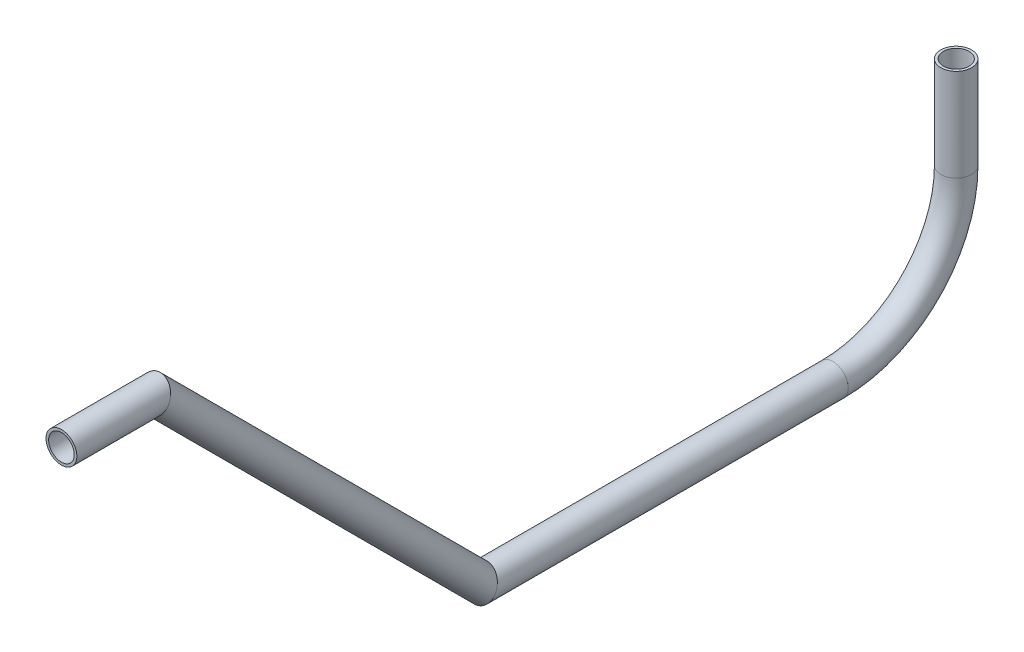
SolidWorks part; units mm, degrees
ref_plane "Front Plane" through (0, 0, 0) normal (0, 0, 1) x (1, 0, 0)
ref_plane "Top Plane" through (0, 0, 0) normal (0, 1, 0) x (1, 0, 0)
ref_plane "Right Plane" through (0, 0, 0) normal (1, 0, 0) x (0, 0, -1)
sketch "Sketch1" plane through (0, 0, 0) normal (1, 0, 0) x (0, 0, -1)
  line L0 (-303.593, 599.7633) -> (-265.493, 599.7633)
  line L2 (-265.493, 599.7633) -> (-130.9227, 465.193)
  line L3 (-130.9227, 465.193) -> (14.1198, 465.193)
  line L4 (64.9198, 554.093) -> (64.9198, 515.993)
  line L5 (-265.493, 599.7633) -> (-145.8362, 599.7633) construction
  arc A0 (14.1198, 465.193) -> (64.9198, 515.993) centre (14.1198, 515.993) ccw
  dimension "D1" = 45
  dimension "D2" = 50.8
  dimension "D3" = 38.1
  dimension "D4" = 38.1
other "Pipe 0.5 SCH 40(1)"
ref_plane "Plane1" through (0, 599.7633, 303.593) normal (0, 0, -1) x (0, 1, 0)
sketch "Sketch11" plane through (0, 599.7633, 303.593) normal (0, 0, -1) x (0, 1, 0)
  circle A0 centre (0, 0) radius 5.2832
  circle A1 centre (0, 0) radius 6.35
  point P5 (0, 0)
  dimension "In_dia" = 10.5664
  dimension "Out_dia" = 12.7
